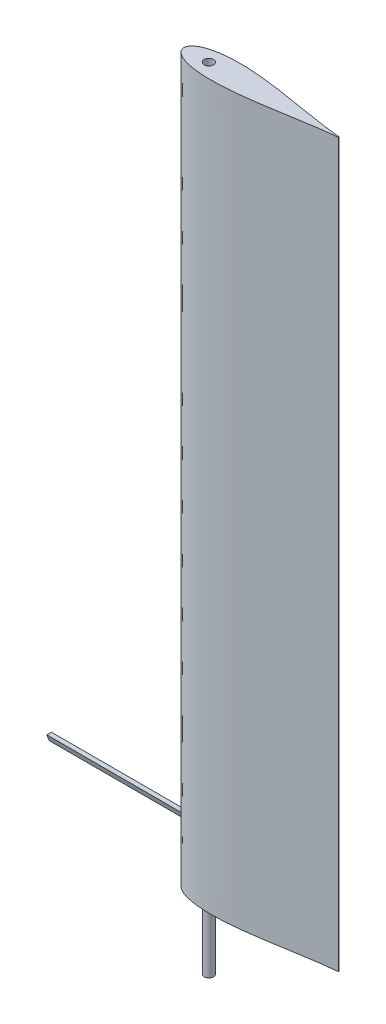
SolidWorks part; units mm, degrees
material "Thornel Mat VMA"
ref_plane "Front Plane" through (0, 0, 0) normal (0, 0, 1) x (1, 0, 0)
ref_plane "Top Plane" through (0, 0, 0) normal (0, 1, 0) x (1, 0, 0)
ref_plane "Right Plane" through (0, 0, 0) normal (1, 0, 0) x (0, 0, -1)
sketch "Sketch2" plane through (0, 0, 0) normal (0, 1, 0) x (1, 0, 0)
  arc A10 (1548.0456, 1052.8481) -> (1549.5016, 1054.4302) centre (1547.9141, 1054.4302) ccw
  arc A12 (990.2438, 1054.4302) -> (1029.1058, 1054.4302) centre (1009.6748, 1054.4302) ccw
  arc A16 (1549.5016, 1054.4302) -> (1548.0456, 1056.0122) centre (1547.9141, 1054.4302) ccw
  arc A22 (1029.1058, 1054.4302) -> (990.2438, 1054.4302) centre (1009.6748, 1054.4302) ccw
  spline S0 degree 3 poles (905.5348, 1054.4302) (905.6529, 1052.6135) (905.8893, 1048.9782) (907.6996, 1043.782) (910.3228, 1038.9891) (914.0085, 1034.16) (918.7483, 1029.452) (924.4831, 1024.9723) (931.6223, 1020.3904) (940.233, 1015.9247) (950.2937, 1011.7245) (960.6051, 1008.1917) (973.1839, 1004.6204) (988.0815, 1001.3116) (1005.2862, 998.4909) (1022.6005, 996.4617) (1039.9786, 995.0993) (1061.2599, 994.1324) (1086.4403, 993.9418) (1115.4775, 994.8248) (1144.4722, 996.61) (1173.4103, 999.1377) (1202.288, 1002.2756) (1235.9097, 1006.517) (1274.2457, 1012.0272) (1317.2823, 1018.8215) (1360.2666, 1025.9367) (1403.2422, 1033.1032) (1446.2572, 1040.0302) (1482.1779, 1045.3335) (1510.9866, 1049.0441) (1530.5409, 1051.2792) (1542.9098, 1052.3878) (1548.0456, 1052.8481) knots 0 0 0 0 0.008131 0.016271 0.024415 0.032563 0.043421 0.054279 0.065137 0.08142 0.097702 0.113985 0.130267 0.156316 0.182366 0.208416 0.234466 0.260516 0.30393 0.347345 0.390761 0.434177 0.477593 0.521009 0.586132 0.651256 0.716381 0.781505 0.846629 0.911752 0.944314 0.976878 1 1 1 1
  spline S1 degree 3 poles (1548.0456, 1056.0122) (1542.9098, 1056.4725) (1530.5409, 1057.5811) (1510.9866, 1059.8162) (1482.1779, 1063.5268) (1446.2572, 1068.8301) (1403.2422, 1075.7571) (1360.2666, 1082.9236) (1317.2823, 1090.0388) (1274.2457, 1096.8331) (1235.9097, 1102.3433) (1202.288, 1106.5848) (1173.4103, 1109.7226) (1144.4722, 1112.2503) (1115.4775, 1114.0356) (1086.4403, 1114.9185) (1061.2599, 1114.728) (1039.9786, 1113.761) (1022.6005, 1112.3986) (1005.2862, 1110.3694) (988.0814, 1107.5487) (973.1839, 1104.2399) (960.6051, 1100.6686) (950.2937, 1097.1358) (940.233, 1092.9356) (931.6223, 1088.4699) (924.4831, 1083.888) (918.7483, 1079.4083) (914.0085, 1074.7003) (910.3228, 1069.8712) (907.6997, 1065.0783) (905.8893, 1059.8821) (905.6529, 1056.2468) (905.5348, 1054.4302) knots 0 0 0 0 0.023122 0.055686 0.088248 0.153371 0.218495 0.283619 0.348744 0.413868 0.478991 0.522407 0.565823 0.609239 0.652655 0.69607 0.739484 0.765534 0.791584 0.817634 0.843684 0.869733 0.886015 0.902298 0.91858 0.934863 0.945721 0.956579 0.967437 0.975585 0.983729 0.991869 1 1 1 1
  point P0 (0, 0)
extrude "Boss-Extrude2" add sketch "Sketch2" along normal blind 2997.2 contours A16 S1 S0 A10 A22 A12
sketch "Sketch3" plane through (0, 0, 0) normal (0, -1, 0) x (1, 0, 0)
  circle A0 centre (1009.6748, -1054.4302) radius 19.05
  dimension "D1" = 38.1
extrude "Boss-Extrude3" add sketch "Sketch3" along normal blind 279.4
ref_plane "Plane1" through (905.5348, 0, 0) normal (1, 0, 0) x (0, 0, -1)
sketch "Sketch4" plane through (905.5348, 0, 0) normal (1, 0, 0) x (0, 0, -1)
  line L0 (1063.9552, 254) -> (1044.9052, 254)
  line L5 (1044.9052, 254) -> (1054.4302, 228.6)
  line L6 (1054.4302, 2997.2) -> (1054.4302, 0) construction
  line L7 (1054.4302, 228.6) -> (1063.9552, 254)
  line L8 (55, 0) -> (-55, 0) construction
  point P7 (1054.4302, 188.0089)
  dimension "D1" = 254
  dimension "D2" = 19.05
  dimension "D3" = 25.4
extrude "Boss-Extrude4" add sketch "Sketch4" against normal blind 558.8 separate body
